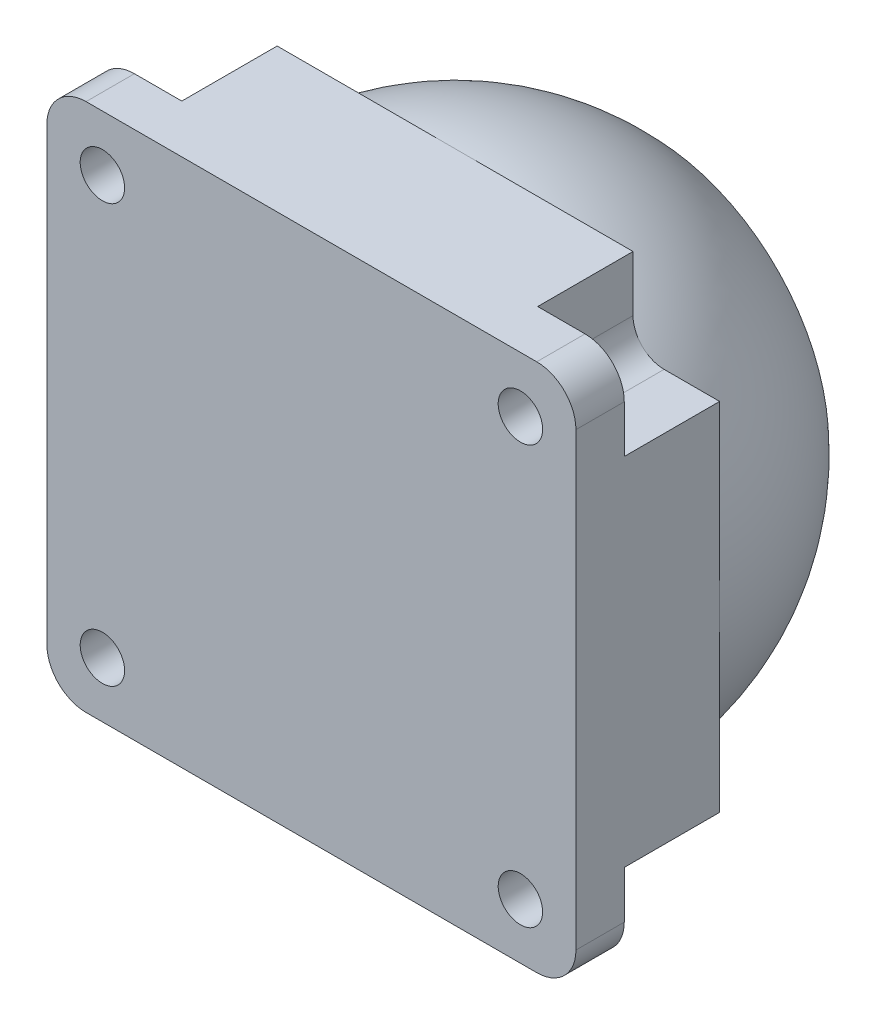
SolidWorks part; units mm, degrees
ref_plane "Спереди" through (0, 0, 0) normal (0, 0, 1) x (1, 0, 0)
ref_plane "Сверху" through (0, 0, 0) normal (0, 1, 0) x (1, 0, 0)
ref_plane "Справа" through (0, 0, 0) normal (1, 0, 0) x (0, 0, -1)
sketch "Эскиз1" plane through (0, 0, 0) normal (0, 0, 1) x (1, 0, 0)
  line L1 (-20.25, 20.25) -> (20.25, 20.25)
  line L2 (-20.25, 20.25) -> (-20.25, -20.25)
  line L3 (-20.25, -20.25) -> (20.25, -20.25)
  line L4 (20.25, 20.25) -> (20.25, -20.25)
  line L5 (-20.25, 20.25) -> (20.25, -20.25) construction
  line L6 (-20.25, -20.25) -> (20.25, 20.25) construction
  point P0 (0, 0)
  dimension "D1" = 40.5
  dimension "D2" = 40.5
extrude "Бобышка-Вытянуть1" add sketch "Эскиз1" along normal blind 11
sketch "Эскиз2" plane through (0, 0, 11) normal (0, 0, 1) x (1, 0, 0)
  line L1 (20.25, 20.25) -> (-20.25, 20.25) construction
  line L2 (-20.25, -20.25) -> (20.25, -20.25) construction
  line L3 (-16, 16) -> (16, 16) construction
  line L4 (-16, 16) -> (-16, -16) construction
  line L7 (-16, -16) -> (16, -16) construction
  line L8 (16, 16) -> (16, -16) construction
  line L9 (0, 20.25) -> (0, -20.25) construction
  line L10 (-16, 16) -> (16, -16) construction
  line L11 (-16, -16) -> (16, 16) construction
  point P0 (0, 0)
  point P16 (-16, 16)
  point P20 (16, 16)
  point P21 (16, -16)
  point P22 (-16, -16)
  point P23 (0, 0)
  dimension "D1" = 32
  dimension "D2" = 32
  dimension "D5" = 4
hole_wizard "Отверстие с зазором M31" positions "Эскиз4" profile "Эскиз5" hole size "M3" standard "Ansi Metric" end condition through all
sketch "Эскиз4" plane through (0, 0, 11) normal (0, 0, 1) x (1, 0, 0)
  point P0 (-16, 16)
  point P3 (16, 16)
  point P6 (16, -16)
  point P9 (-16, -16)
sketch "Эскиз5" plane through (-16, 16, 11) normal (1, 0, 0) x (0, -1, 0)
  line L0 (0, 0) -> (0, 11)
  line L1 (0, 11) -> (1.7, 11)
  line L2 (1.7, 11) -> (1.7, 0)
  line L5 (1.7, 0) -> (0, 0)
  line L11 (0, -6.35) -> (0, 107.95) construction
  dimension "Диаметр сквозного отверстия" = 3.4
  dimension "Глубина сквозного отверстия" = 11
ref_plane "Плоскость1" through (0, 0, 0) normal (0, -1, 0) x (-1, 0, 0)
sketch "Эскиз6" plane through (0, 0, 0) normal (0, -1, 0) x (-1, 0, 0)
  line L0 (20.25, 0) -> (0, 0)
  line L1 (0, 0) -> (0, 20.25)
  arc A0 (20.25, 0) -> (0, 20.25) centre (0, 0) ccw
revolve "Повернуть1" add sketch "Эскиз6" angle 360 about L1
ref_plane "Плоскость2" through (0, 0, -15) normal (0, 0, -1) x (-1, 0, 0)
sketch "Эскиз7" plane through (0, 0, -15) normal (0, 0, -1) x (-1, 0, 0)
  line L1 (-20.25, 20.25) -> (20.25, 20.25)
  line L2 (-20.25, 20.25) -> (-20.25, -20.25)
  line L3 (-20.25, -20.25) -> (20.25, -20.25)
  line L4 (20.25, 20.25) -> (20.25, -20.25)
  line L5 (-20.25, 20.25) -> (20.25, -20.25) construction
  line L6 (-20.25, -20.25) -> (20.25, 20.25) construction
  point P0 (0, 0)
extrude "Вырез-Вытянуть1" cut sketch "Эскиз7" along normal blind 11
sketch "Эскиз9" plane through (0, 0, 0) normal (0, 0, -1) x (-1, 0, 0)
  line L0 (-20.25, 13.6226) -> (-13.6226, 13.6226) construction
  line L1 (-20.25, 20.25) -> (-13.6226, 20.25)
  line L2 (-20.25, 20.25) -> (-20.25, 13.6226)
  line L3 (-20.25, 13.6226) -> (-16, 13.6226)
  line L4 (-13.6226, 20.25) -> (-13.6226, 16)
  line L5 (-13.6226, 13.6226) -> (-13.6226, 20.25) construction
  line L6 (20.25, 20.25) -> (20.25, 13.6226)
  line L7 (20.25, 20.25) -> (13.6226, 20.25)
  line L8 (13.6226, 20.25) -> (13.6226, 16)
  line L9 (20.25, 13.6226) -> (16, 13.6226)
  line L10 (13.6226, 20.25) -> (13.6226, 13.6226) construction
  line L11 (13.6226, 13.6226) -> (20.25, 13.6226) construction
  line L12 (20.25, -20.25) -> (13.6226, -20.25)
  line L13 (20.25, -20.25) -> (20.25, -13.6226)
  line L14 (20.25, -13.6226) -> (16, -13.6226)
  line L15 (13.6226, -20.25) -> (13.6226, -16)
  line L16 (20.25, -13.6226) -> (13.6226, -13.6226) construction
  line L17 (13.6226, -13.6226) -> (13.6226, -20.25) construction
  line L18 (-20.25, -20.25) -> (-20.25, -13.6226)
  line L19 (-20.25, -20.25) -> (-13.6226, -20.25)
  line L20 (-13.6226, -20.25) -> (-13.6226, -16)
  line L21 (-20.25, -13.6226) -> (-16, -13.6226)
  line L22 (-13.6226, -20.25) -> (-13.6226, -13.6226) construction
  line L23 (-13.6226, -13.6226) -> (-20.25, -13.6226) construction
  arc A0 (-16, 13.6226) -> (-13.6226, 16) centre (-16, 16) ccw
  arc A1 (0, 20.25) -> (-20.25, 0) centre (0, 0) ccw construction
  arc A2 (13.6226, 16) -> (16, 13.6226) centre (16, 16) ccw
  arc A3 (16, -13.6226) -> (13.6226, -16) centre (16, -16) ccw
  arc A4 (-13.6226, -16) -> (-16, -13.6226) centre (-16, -16) ccw
  point P32 (0.2296, -0.1166)
  point P37 (0, 0)
  dimension "D1" = 4
extrude "Вырез-Вытянуть2" cut sketch "Эскиз9" against normal blind 7.3
fillet "Скругление1" radius 3 4 edges at (20.25, -20.25, 9.15) (-20.25, -20.25, 9.15) (-20.25, 20.25, 9.15) (20.25, 20.25, 9.15)
